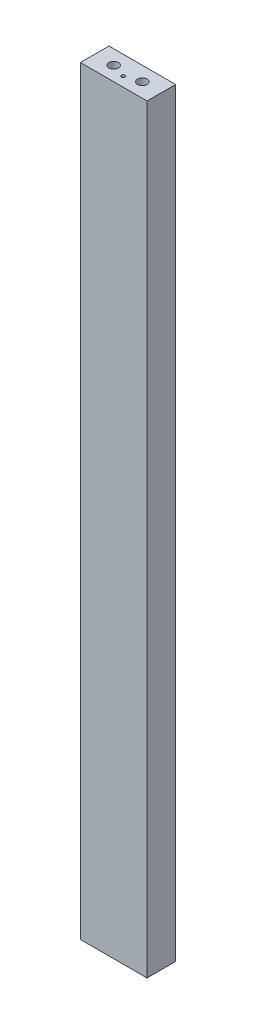
SolidWorks part; units mm, degrees
ref_plane "Front Plane" through (0, 0, 0) normal (0, 0, 1) x (1, 0, 0)
ref_plane "Top Plane" through (0, 0, 0) normal (0, 1, 0) x (1, 0, 0)
ref_plane "Right Plane" through (0, 0, 0) normal (1, 0, 0) x (0, 0, -1)
sketch "Sketch1" plane through (0, 0, 0) normal (0, 1, 0) x (1, 0, 0)
  line L1 (0, 0) -> (88.9, 0)
  line L2 (0, 0) -> (0, -38.1)
  line L3 (0, -38.1) -> (88.9, -38.1)
  line L4 (88.9, 0) -> (88.9, -38.1)
  dimension "D1" = 38.1
  dimension "D2" = 88.9
extrude "Boss-Extrude1" add sketch "Sketch1" along normal blind 1012.825
sketch "Sketch2" plane through (0, 1012.825, 0) normal (0, 1, 0) x (1, 0, 0)
  line L0 (25.4, -19.05) -> (63.5, -19.05) construction
  line L1 (0, 0) -> (0, -38.1) construction
  line L2 (88.9, 0) -> (0, 0) construction
  circle A0 centre (25.4, -19.05) radius 6.35
  circle A1 centre (63.5, -19.05) radius 6.35
  point P7 (0, -19.05)
  point P10 (44.45, 0)
  point P11 (44.45, -19.05)
  dimension "D1" = 12.7
  dimension "D2" = 12.7
  dimension "D3" = 38.1
extrude "Cut-Extrude1" cut sketch "Sketch2" against normal blind 19.05
sketch "Sketch3" plane through (0, 0, 0) normal (0, -1, 0) x (1, 0, 0)
  line L0 (25.4, 19.05) -> (63.5, 19.05) construction
  line L3 (0, 0) -> (0, 38.1) construction
  line L4 (0, 38.1) -> (88.9, 38.1) construction
  circle A0 centre (25.4, 19.05) radius 6.35
  circle A1 centre (63.5, 19.05) radius 6.35
  point P8 (0, 19.05)
  point P11 (44.45, 19.05)
  point P12 (44.45, 38.1)
  dimension "D1" = 12.7
  dimension "D2" = 12.7
  dimension "D3" = 38.1
extrude "Cut-Extrude2" cut sketch "Sketch3" against normal blind 19.05
sketch "Sketch4" plane through (0, 0, 0) normal (0, -1, 0) x (1, 0, 0)
  line L1 (0, 38.1) -> (88.9, 38.1) construction
  line L2 (88.9, 38.1) -> (88.9, 0) construction
  point P0 (76.2, 25.4)
  point P1 (12.7, 19.05)
  dimension "D1" = 12.7
  dimension "D2" = 12.7
  dimension "D3" = 19.05
  dimension "D4" = 76.2
sketch "Sketch5" plane through (0, 1012.825, 0) normal (0, 1, 0) x (1, 0, 0)
  line L0 (88.9, -38.1) -> (88.9, 0) construction
  line L1 (88.9, 0) -> (0, 0) construction
  point P0 (44.45, -25.4)
  dimension "D1" = 44.45
  dimension "D2" = 25.4
hole_wizard "#10 (0.1935) Diameter Hole1" positions "3DSketch1" profile "Sketch7" hole size "#10" standard "ANSI Inch"
sketch3d "3DSketch1"
  point P0 (44.45, 1012.825, 25.4)
  point P3 (12.7, 0, 19.05)
  point P6 (76.2, 0, 25.4)
sketch "Sketch7" plane through (44.45, 1012.825, 25.4) normal (1, 0, 0) x (0, 0, 1)
  line L0 (0, 0) -> (0, 77.6766)
  line L1 (0, 77.6766) -> (2.4574, 76.2)
  line L2 (2.4574, 76.2) -> (2.4574, 0)
  line L5 (2.4574, 0) -> (0, 0)
  line L10 (0, 77.6766) -> (-2.4575, 76.2) construction
  line L11 (0, -6.35) -> (0, 107.95) construction
  dimension "Hole Dia." = 4.9149
  dimension "Hole Depth" = 76.2
  dimension "Drill Angle" = 118
